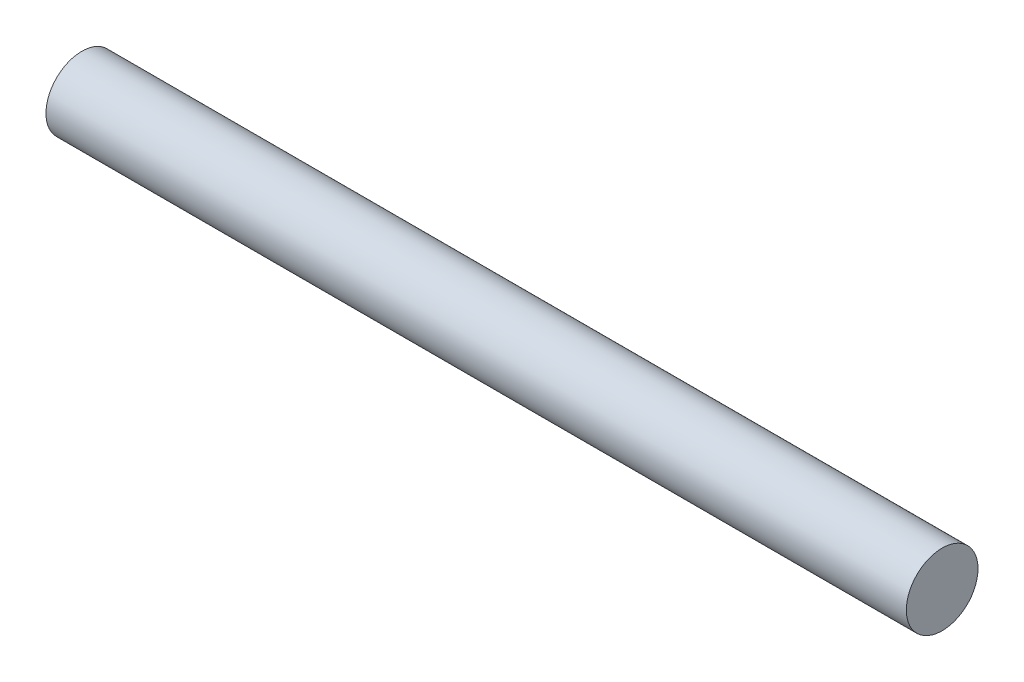
SolidWorks part; units mm, degrees
material "Alloy Steel"
ref_plane "Front Plane" through (0, 0, 0) normal (0, 0, 1) x (1, 0, 0)
ref_plane "Top Plane" through (0, 0, 0) normal (0, 1, 0) x (1, 0, 0)
ref_plane "Right Plane" through (0, 0, 0) normal (1, 0, 0) x (0, 0, -1)
sketch "Sketch1" plane through (0, 0, 0) normal (1, 0, 0) x (0, 0, -1)
  circle A0 centre (0, 0) radius 1.5875
  dimension "D1" = 3.175
extrude "Boss-Extrude1" add sketch "Sketch1" along normal mid plane 38.1
